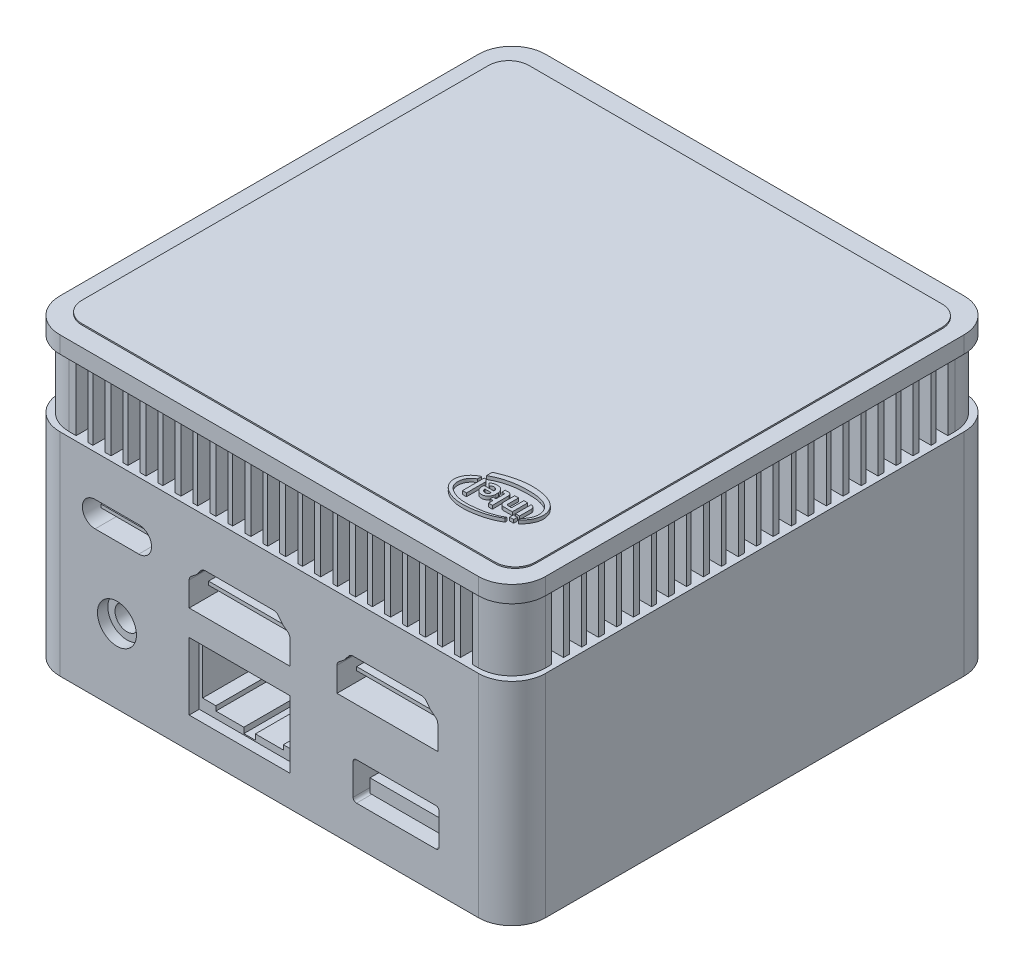
SolidWorks part; units mm, degrees
ref_plane "前视基准面" through (0, 0, 0) normal (0, 0, 1) x (1, 0, 0)
ref_plane "上视基准面" through (0, 0, 0) normal (0, 1, 0) x (1, 0, 0)
ref_plane "右视基准面" through (0, 0, 0) normal (1, 0, 0) x (0, 0, -1)
sketch "草图1" plane through (0, 0, 0) normal (0, 1, 0) x (1, 0, 0)
  line L1 (-31.15, 36.15) -> (31.15, 36.15)
  line L2 (-36.15, 31.15) -> (-36.15, -31.15)
  line L3 (-31.15, -36.15) -> (31.15, -36.15)
  line L4 (36.15, 31.15) -> (36.15, -31.15)
  line L5 (-36.15, 36.15) -> (36.15, -36.15) construction
  line L6 (-36.15, -36.15) -> (36.15, 36.15) construction
  arc A0 (31.15, -36.15) -> (36.15, -31.15) centre (31.15, -31.15) ccw
  arc A1 (-36.15, -31.15) -> (-31.15, -36.15) centre (-31.15, -31.15) ccw
  arc A2 (-31.15, 36.15) -> (-36.15, 31.15) centre (-31.15, 31.15) ccw
  arc A3 (31.15, 36.15) -> (36.15, 31.15) centre (31.15, 31.15) cw
  point P0 (0, 0)
  dimension "D2" = 5
  dimension "D3" = 5
  dimension "D4" = 5
  dimension "D5" = 5
  dimension "D1" = 72.3
extrude "凸台-拉伸1" add sketch "草图1" along normal blind 31.5
sketch "草图2" plane through (0, 31.5, 0) normal (0, 1, 0) x (1, 0, 0)
  line L1 (-30.45, 35.45) -> (30.45, 35.45)
  line L2 (-35.45, 30.45) -> (-35.45, -30.45)
  line L3 (-30.45, -35.45) -> (30.45, -35.45)
  line L4 (35.45, 30.45) -> (35.45, -30.45)
  line L5 (-35.45, 35.45) -> (35.45, -35.45) construction
  line L6 (-35.45, -35.45) -> (35.45, 35.45) construction
  arc A0 (-30.45, 35.45) -> (-35.45, 30.45) centre (-30.45, 30.45) ccw
  arc A1 (-35.45, -30.45) -> (-30.45, -35.45) centre (-30.45, -30.45) ccw
  arc A2 (30.45, -35.45) -> (35.45, -30.45) centre (30.45, -30.45) ccw
  arc A3 (30.45, 35.45) -> (35.45, 30.45) centre (30.45, 30.45) cw
  point P0 (0, 0)
  dimension "D2" = 5
  dimension "D3" = 5
  dimension "D4" = 5
  dimension "D5" = 5
  dimension "D1" = 70.9
extrude "凸台-拉伸2" add sketch "草图2" along normal blind 10
sketch "草图3" plane through (0, 41.5, 0) normal (0, 1, 0) x (1, 0, 0)
  line L0 (30.45, 35.45) -> (-30.45, 35.45) construction
  line L1 (-29.5755, 37.7794) -> (-27.7755, 37.7794)
  line L2 (-29.5755, 37.7794) -> (-29.5755, 33.1206)
  line L3 (-29.5755, 33.1206) -> (-27.7755, 33.1206)
  line L4 (-27.7755, 37.7794) -> (-27.7755, 33.1206)
  line L5 (-29.5755, 37.7794) -> (-27.7755, 33.1206) construction
  line L6 (-29.5755, 33.1206) -> (-27.7755, 37.7794) construction
  line L7 (-26.8755, 37.7794) -> (-25.0755, 37.7794)
  line L8 (-26.8755, 37.7794) -> (-26.8755, 33.1206)
  line L9 (-26.8755, 33.1206) -> (-25.0755, 33.1206)
  line L10 (-25.0755, 37.7794) -> (-25.0755, 33.1206)
  line L11 (-21.6755, 37.7794) -> (-19.8755, 37.7794)
  line L12 (-19.8755, 37.7794) -> (-19.8755, 33.1206)
  line L13 (-21.6755, 33.1206) -> (-19.8755, 33.1206)
  line L14 (-21.6755, 37.7794) -> (-21.6755, 33.1206)
  line L15 (-24.3755, 37.7794) -> (-24.3755, 33.1206)
  line L16 (-24.3755, 37.7794) -> (-22.5755, 37.7794)
  line L17 (-22.5755, 37.7794) -> (-22.5755, 33.1206)
  line L18 (-24.3755, 33.1206) -> (-22.5755, 33.1206)
  line L19 (-16.4755, 37.7794) -> (-14.6755, 37.7794)
  line L20 (-14.6755, 37.7794) -> (-14.6755, 33.1206)
  line L21 (-16.4755, 33.1206) -> (-14.6755, 33.1206)
  line L22 (-16.4755, 37.7794) -> (-16.4755, 33.1206)
  line L23 (-19.1755, 37.7794) -> (-19.1755, 33.1206)
  line L24 (-19.1755, 37.7794) -> (-17.3755, 37.7794)
  line L25 (-17.3755, 37.7794) -> (-17.3755, 33.1206)
  line L26 (-19.1755, 33.1206) -> (-17.3755, 33.1206)
  line L27 (-11.2755, 37.7794) -> (-9.4755, 37.7794)
  line L28 (-9.4755, 37.7794) -> (-9.4755, 33.1206)
  line L29 (-11.2755, 33.1206) -> (-9.4755, 33.1206)
  line L30 (-11.2755, 37.7794) -> (-11.2755, 33.1206)
  line L31 (-13.9755, 37.7794) -> (-13.9755, 33.1206)
  line L32 (-13.9755, 37.7794) -> (-12.1755, 37.7794)
  line L33 (-12.1755, 37.7794) -> (-12.1755, 33.1206)
  line L34 (-13.9755, 33.1206) -> (-12.1755, 33.1206)
  line L35 (-6.0755, 37.7794) -> (-4.2755, 37.7794)
  line L36 (-4.2755, 37.7794) -> (-4.2755, 33.1206)
  line L37 (-6.0755, 33.1206) -> (-4.2755, 33.1206)
  line L38 (-6.0755, 37.7794) -> (-6.0755, 33.1206)
  line L39 (-8.7755, 37.7794) -> (-8.7755, 33.1206)
  line L40 (-8.7755, 37.7794) -> (-6.9755, 37.7794)
  line L41 (-6.9755, 37.7794) -> (-6.9755, 33.1206)
  line L42 (-8.7755, 33.1206) -> (-6.9755, 33.1206)
  line L43 (-0.8755, 37.7794) -> (0.9245, 37.7794)
  line L44 (0.9245, 37.7794) -> (0.9245, 33.1206)
  line L45 (-0.8755, 33.1206) -> (0.9245, 33.1206)
  line L46 (-0.8755, 37.7794) -> (-0.8755, 33.1206)
  line L47 (-3.5755, 37.7794) -> (-3.5755, 33.1206)
  line L48 (-3.5755, 37.7794) -> (-1.7755, 37.7794)
  line L49 (-1.7755, 37.7794) -> (-1.7755, 33.1206)
  line L50 (-3.5755, 33.1206) -> (-1.7755, 33.1206)
  line L51 (4.3245, 37.7794) -> (6.1245, 37.7794)
  line L52 (6.1245, 37.7794) -> (6.1245, 33.1206)
  line L53 (4.3245, 33.1206) -> (6.1245, 33.1206)
  line L54 (4.3245, 37.7794) -> (4.3245, 33.1206)
  line L55 (1.6245, 37.7794) -> (1.6245, 33.1206)
  line L56 (1.6245, 37.7794) -> (3.4245, 37.7794)
  line L57 (3.4245, 37.7794) -> (3.4245, 33.1206)
  line L58 (1.6245, 33.1206) -> (3.4245, 33.1206)
  line L59 (9.5245, 37.7794) -> (11.3245, 37.7794)
  line L60 (11.3245, 37.7794) -> (11.3245, 33.1206)
  line L61 (9.5245, 33.1206) -> (11.3245, 33.1206)
  line L62 (9.5245, 37.7794) -> (9.5245, 33.1206)
  line L63 (6.8245, 37.7794) -> (6.8245, 33.1206)
  line L64 (6.8245, 37.7794) -> (8.6245, 37.7794)
  line L65 (8.6245, 37.7794) -> (8.6245, 33.1206)
  line L66 (6.8245, 33.1206) -> (8.6245, 33.1206)
  line L67 (14.7245, 37.7794) -> (16.5245, 37.7794)
  line L68 (16.5245, 37.7794) -> (16.5245, 33.1206)
  line L69 (14.7245, 33.1206) -> (16.5245, 33.1206)
  line L70 (14.7245, 37.7794) -> (14.7245, 33.1206)
  line L71 (12.0245, 37.7794) -> (12.0245, 33.1206)
  line L72 (12.0245, 37.7794) -> (13.8245, 37.7794)
  line L73 (13.8245, 37.7794) -> (13.8245, 33.1206)
  line L74 (12.0245, 33.1206) -> (13.8245, 33.1206)
  line L75 (19.9245, 37.7794) -> (21.7245, 37.7794)
  line L76 (21.7245, 37.7794) -> (21.7245, 33.1206)
  line L77 (19.9245, 33.1206) -> (21.7245, 33.1206)
  line L78 (19.9245, 37.7794) -> (19.9245, 33.1206)
  line L79 (17.2245, 37.7794) -> (17.2245, 33.1206)
  line L80 (17.2245, 37.7794) -> (19.0245, 37.7794)
  line L81 (19.0245, 37.7794) -> (19.0245, 33.1206)
  line L82 (17.2245, 33.1206) -> (19.0245, 33.1206)
  line L83 (25.1245, 37.7794) -> (26.9245, 37.7794)
  line L84 (26.9245, 37.7794) -> (26.9245, 33.1206)
  line L85 (25.1245, 33.1206) -> (26.9245, 33.1206)
  line L86 (25.1245, 37.7794) -> (25.1245, 33.1206)
  line L87 (22.4245, 37.7794) -> (22.4245, 33.1206)
  line L88 (22.4245, 37.7794) -> (24.2245, 37.7794)
  line L89 (24.2245, 37.7794) -> (24.2245, 33.1206)
  line L90 (22.4245, 33.1206) -> (24.2245, 33.1206)
  line L95 (27.6245, 37.7794) -> (27.6245, 33.1206)
  line L96 (27.6245, 37.7794) -> (29.4245, 37.7794)
  line L97 (29.4245, 37.7794) -> (29.4245, 33.1206)
  line L98 (27.6245, 33.1206) -> (29.4245, 33.1206)
  line L99 (30.3245, 37.7794) -> (32.1245, 37.7794) [skipped]
  line L100 (32.1245, 37.7794) -> (32.1245, 33.1206) [skipped]
  line L101 (30.3245, 33.1206) -> (32.1245, 33.1206) [skipped]
  line L102 (30.3245, 37.7794) -> (30.3245, 33.1206) [skipped]
  line L103 (0, 0) -> (30.3531, 30.3531) construction
  line L104 (0, 0) -> (-19.9439, 19.9439) construction
  line L105 (-33.1206, 29.5755) -> (-37.7794, 27.7755) construction
  line L106 (-37.7794, 29.5755) -> (-33.1206, 27.7755) construction
  line L107 (-33.1206, -27.6245) -> (-33.1206, -29.4245)
  line L108 (-37.7794, -29.4245) -> (-33.1206, -29.4245)
  line L109 (-37.7794, -27.6245) -> (-37.7794, -29.4245)
  line L110 (-37.7794, -27.6245) -> (-33.1206, -27.6245)
  line L111 (-33.1206, -22.4245) -> (-33.1206, -24.2245)
  line L112 (-37.7794, -24.2245) -> (-33.1206, -24.2245)
  line L113 (-37.7794, -22.4245) -> (-37.7794, -24.2245)
  line L114 (-37.7794, -22.4245) -> (-33.1206, -22.4245)
  line L115 (-37.7794, -25.1245) -> (-33.1206, -25.1245)
  line L116 (-33.1206, -25.1245) -> (-33.1206, -26.9245)
  line L117 (-37.7794, -26.9245) -> (-33.1206, -26.9245)
  line L118 (-37.7794, -25.1245) -> (-37.7794, -26.9245)
  line L119 (-33.1206, -17.2245) -> (-33.1206, -19.0245)
  line L120 (-37.7794, -19.0245) -> (-33.1206, -19.0245)
  line L121 (-37.7794, -17.2245) -> (-37.7794, -19.0245)
  line L122 (-37.7794, -17.2245) -> (-33.1206, -17.2245)
  line L123 (-37.7794, -19.9245) -> (-33.1206, -19.9245)
  line L124 (-33.1206, -19.9245) -> (-33.1206, -21.7245)
  line L125 (-37.7794, -21.7245) -> (-33.1206, -21.7245)
  line L126 (-37.7794, -19.9245) -> (-37.7794, -21.7245)
  line L127 (-33.1206, -12.0245) -> (-33.1206, -13.8245)
  line L128 (-37.7794, -13.8245) -> (-33.1206, -13.8245)
  line L129 (-37.7794, -12.0245) -> (-37.7794, -13.8245)
  line L130 (-37.7794, -12.0245) -> (-33.1206, -12.0245)
  line L131 (-37.7794, -14.7245) -> (-33.1206, -14.7245)
  line L132 (-33.1206, -14.7245) -> (-33.1206, -16.5245)
  line L133 (-37.7794, -16.5245) -> (-33.1206, -16.5245)
  line L134 (-37.7794, -14.7245) -> (-37.7794, -16.5245)
  line L135 (-33.1206, -6.8245) -> (-33.1206, -8.6245)
  line L136 (-37.7794, -8.6245) -> (-33.1206, -8.6245)
  line L137 (-37.7794, -6.8245) -> (-37.7794, -8.6245)
  line L138 (-37.7794, -6.8245) -> (-33.1206, -6.8245)
  line L139 (-37.7794, -9.5245) -> (-33.1206, -9.5245)
  line L140 (-33.1206, -9.5245) -> (-33.1206, -11.3245)
  line L141 (-37.7794, -11.3245) -> (-33.1206, -11.3245)
  line L142 (-37.7794, -9.5245) -> (-37.7794, -11.3245)
  line L143 (-33.1206, -1.6245) -> (-33.1206, -3.4245)
  line L144 (-37.7794, -3.4245) -> (-33.1206, -3.4245)
  line L145 (-37.7794, -1.6245) -> (-37.7794, -3.4245)
  line L146 (-37.7794, -1.6245) -> (-33.1206, -1.6245)
  line L147 (-37.7794, -4.3245) -> (-33.1206, -4.3245)
  line L148 (-33.1206, -4.3245) -> (-33.1206, -6.1245)
  line L149 (-37.7794, -6.1245) -> (-33.1206, -6.1245)
  line L150 (-37.7794, -4.3245) -> (-37.7794, -6.1245)
  line L151 (-33.1206, 3.5755) -> (-33.1206, 1.7755)
  line L152 (-37.7794, 1.7755) -> (-33.1206, 1.7755)
  line L153 (-37.7794, 3.5755) -> (-37.7794, 1.7755)
  line L154 (-37.7794, 3.5755) -> (-33.1206, 3.5755)
  line L155 (-37.7794, 0.8755) -> (-33.1206, 0.8755)
  line L156 (-33.1206, 0.8755) -> (-33.1206, -0.9245)
  line L157 (-37.7794, -0.9245) -> (-33.1206, -0.9245)
  line L158 (-37.7794, 0.8755) -> (-37.7794, -0.9245)
  line L159 (-33.1206, 8.7755) -> (-33.1206, 6.9755)
  line L160 (-37.7794, 6.9755) -> (-33.1206, 6.9755)
  line L161 (-37.7794, 8.7755) -> (-37.7794, 6.9755)
  line L162 (-37.7794, 8.7755) -> (-33.1206, 8.7755)
  line L163 (-37.7794, 6.0755) -> (-33.1206, 6.0755)
  line L164 (-33.1206, 6.0755) -> (-33.1206, 4.2755)
  line L165 (-37.7794, 4.2755) -> (-33.1206, 4.2755)
  line L166 (-37.7794, 6.0755) -> (-37.7794, 4.2755)
  line L167 (-33.1206, 13.9755) -> (-33.1206, 12.1755)
  line L168 (-37.7794, 12.1755) -> (-33.1206, 12.1755)
  line L169 (-37.7794, 13.9755) -> (-37.7794, 12.1755)
  line L170 (-37.7794, 13.9755) -> (-33.1206, 13.9755)
  line L171 (-37.7794, 11.2755) -> (-33.1206, 11.2755)
  line L172 (-33.1206, 11.2755) -> (-33.1206, 9.4755)
  line L173 (-37.7794, 9.4755) -> (-33.1206, 9.4755)
  line L174 (-37.7794, 11.2755) -> (-37.7794, 9.4755)
  line L175 (-33.1206, 19.1755) -> (-33.1206, 17.3755)
  line L176 (-37.7794, 17.3755) -> (-33.1206, 17.3755)
  line L177 (-37.7794, 19.1755) -> (-37.7794, 17.3755)
  line L178 (-37.7794, 19.1755) -> (-33.1206, 19.1755)
  line L179 (-37.7794, 16.4755) -> (-33.1206, 16.4755)
  line L180 (-33.1206, 16.4755) -> (-33.1206, 14.6755)
  line L181 (-37.7794, 14.6755) -> (-33.1206, 14.6755)
  line L182 (-37.7794, 16.4755) -> (-37.7794, 14.6755)
  line L183 (-33.1206, 24.3755) -> (-33.1206, 22.5755)
  line L184 (-37.7794, 22.5755) -> (-33.1206, 22.5755)
  line L185 (-37.7794, 24.3755) -> (-37.7794, 22.5755)
  line L186 (-37.7794, 24.3755) -> (-33.1206, 24.3755)
  line L187 (-37.7794, 21.6755) -> (-33.1206, 21.6755)
  line L188 (-33.1206, 21.6755) -> (-33.1206, 19.8755)
  line L189 (-37.7794, 19.8755) -> (-33.1206, 19.8755)
  line L190 (-37.7794, 21.6755) -> (-37.7794, 19.8755)
  line L191 (-37.7794, 25.0755) -> (-33.1206, 25.0755)
  line L192 (-33.1206, 26.8755) -> (-33.1206, 25.0755)
  line L193 (-37.7794, 26.8755) -> (-33.1206, 26.8755)
  line L194 (-37.7794, 26.8755) -> (-37.7794, 25.0755)
  line L195 (-37.7794, 27.7755) -> (-33.1206, 27.7755)
  line L196 (-33.1206, 29.5755) -> (-33.1206, 27.7755)
  line L197 (-37.7794, 29.5755) -> (-33.1206, 29.5755)
  line L198 (-37.7794, 29.5755) -> (-37.7794, 27.7755)
  line L199 (29.5755, -37.7794) -> (27.7755, -33.1206) construction
  line L200 (29.5755, -33.1206) -> (27.7755, -37.7794) construction
  line L201 (29.5755, -37.7794) -> (27.7755, -37.7794)
  line L202 (29.5755, -37.7794) -> (29.5755, -33.1206)
  line L203 (29.5755, -33.1206) -> (27.7755, -33.1206)
  line L204 (27.7755, -37.7794) -> (27.7755, -33.1206)
  line L205 (26.8755, -37.7794) -> (25.0755, -37.7794)
  line L206 (26.8755, -37.7794) -> (26.8755, -33.1206)
  line L207 (26.8755, -33.1206) -> (25.0755, -33.1206)
  line L208 (25.0755, -37.7794) -> (25.0755, -33.1206)
  line L209 (21.6755, -37.7794) -> (19.8755, -37.7794)
  line L210 (19.8755, -37.7794) -> (19.8755, -33.1206)
  line L211 (21.6755, -33.1206) -> (19.8755, -33.1206)
  line L212 (21.6755, -37.7794) -> (21.6755, -33.1206)
  line L213 (24.3755, -37.7794) -> (24.3755, -33.1206)
  line L214 (24.3755, -37.7794) -> (22.5755, -37.7794)
  line L215 (22.5755, -37.7794) -> (22.5755, -33.1206)
  line L216 (24.3755, -33.1206) -> (22.5755, -33.1206)
  line L217 (16.4755, -37.7794) -> (14.6755, -37.7794)
  line L218 (14.6755, -37.7794) -> (14.6755, -33.1206)
  line L219 (16.4755, -33.1206) -> (14.6755, -33.1206)
  line L220 (16.4755, -37.7794) -> (16.4755, -33.1206)
  line L221 (19.1755, -37.7794) -> (19.1755, -33.1206)
  line L222 (19.1755, -37.7794) -> (17.3755, -37.7794)
  line L223 (17.3755, -37.7794) -> (17.3755, -33.1206)
  line L224 (19.1755, -33.1206) -> (17.3755, -33.1206)
  line L225 (11.2755, -37.7794) -> (9.4755, -37.7794)
  line L226 (9.4755, -37.7794) -> (9.4755, -33.1206)
  line L227 (11.2755, -33.1206) -> (9.4755, -33.1206)
  line L228 (11.2755, -37.7794) -> (11.2755, -33.1206)
  line L229 (13.9755, -37.7794) -> (13.9755, -33.1206)
  line L230 (13.9755, -37.7794) -> (12.1755, -37.7794)
  line L231 (12.1755, -37.7794) -> (12.1755, -33.1206)
  line L232 (13.9755, -33.1206) -> (12.1755, -33.1206)
  line L233 (6.0755, -37.7794) -> (4.2755, -37.7794)
  line L234 (4.2755, -37.7794) -> (4.2755, -33.1206)
  line L235 (6.0755, -33.1206) -> (4.2755, -33.1206)
  line L236 (6.0755, -37.7794) -> (6.0755, -33.1206)
  line L237 (8.7755, -37.7794) -> (8.7755, -33.1206)
  line L238 (8.7755, -37.7794) -> (6.9755, -37.7794)
  line L239 (6.9755, -37.7794) -> (6.9755, -33.1206)
  line L240 (8.7755, -33.1206) -> (6.9755, -33.1206)
  line L241 (0.8755, -37.7794) -> (-0.9245, -37.7794)
  line L242 (-0.9245, -37.7794) -> (-0.9245, -33.1206)
  line L243 (0.8755, -33.1206) -> (-0.9245, -33.1206)
  line L244 (0.8755, -37.7794) -> (0.8755, -33.1206)
  line L245 (3.5755, -37.7794) -> (3.5755, -33.1206)
  line L246 (3.5755, -37.7794) -> (1.7755, -37.7794)
  line L247 (1.7755, -37.7794) -> (1.7755, -33.1206)
  line L248 (3.5755, -33.1206) -> (1.7755, -33.1206)
  line L249 (-4.3245, -37.7794) -> (-6.1245, -37.7794)
  line L250 (-6.1245, -37.7794) -> (-6.1245, -33.1206)
  line L251 (-4.3245, -33.1206) -> (-6.1245, -33.1206)
  line L252 (-4.3245, -37.7794) -> (-4.3245, -33.1206)
  line L253 (-1.6245, -37.7794) -> (-1.6245, -33.1206)
  line L254 (-1.6245, -37.7794) -> (-3.4245, -37.7794)
  line L255 (-3.4245, -37.7794) -> (-3.4245, -33.1206)
  line L256 (-1.6245, -33.1206) -> (-3.4245, -33.1206)
  line L257 (-9.5245, -37.7794) -> (-11.3245, -37.7794)
  line L258 (-11.3245, -37.7794) -> (-11.3245, -33.1206)
  line L259 (-9.5245, -33.1206) -> (-11.3245, -33.1206)
  line L260 (-9.5245, -37.7794) -> (-9.5245, -33.1206)
  line L261 (-6.8245, -37.7794) -> (-6.8245, -33.1206)
  line L262 (-6.8245, -37.7794) -> (-8.6245, -37.7794)
  line L263 (-8.6245, -37.7794) -> (-8.6245, -33.1206)
  line L264 (-6.8245, -33.1206) -> (-8.6245, -33.1206)
  line L265 (-14.7245, -37.7794) -> (-16.5245, -37.7794)
  line L266 (-16.5245, -37.7794) -> (-16.5245, -33.1206)
  line L267 (-14.7245, -33.1206) -> (-16.5245, -33.1206)
  line L268 (-14.7245, -37.7794) -> (-14.7245, -33.1206)
  line L269 (-12.0245, -37.7794) -> (-12.0245, -33.1206)
  line L270 (-12.0245, -37.7794) -> (-13.8245, -37.7794)
  line L271 (-13.8245, -37.7794) -> (-13.8245, -33.1206)
  line L272 (-12.0245, -33.1206) -> (-13.8245, -33.1206)
  line L273 (-19.9245, -37.7794) -> (-21.7245, -37.7794)
  line L274 (-21.7245, -37.7794) -> (-21.7245, -33.1206)
  line L275 (-19.9245, -33.1206) -> (-21.7245, -33.1206)
  line L276 (-19.9245, -37.7794) -> (-19.9245, -33.1206)
  line L277 (-17.2245, -37.7794) -> (-17.2245, -33.1206)
  line L278 (-17.2245, -37.7794) -> (-19.0245, -37.7794)
  line L279 (-19.0245, -37.7794) -> (-19.0245, -33.1206)
  line L280 (-17.2245, -33.1206) -> (-19.0245, -33.1206)
  line L281 (-25.1245, -37.7794) -> (-26.9245, -37.7794)
  line L282 (-26.9245, -37.7794) -> (-26.9245, -33.1206)
  line L283 (-25.1245, -33.1206) -> (-26.9245, -33.1206)
  line L284 (-25.1245, -37.7794) -> (-25.1245, -33.1206)
  line L285 (-22.4245, -37.7794) -> (-22.4245, -33.1206)
  line L286 (-22.4245, -37.7794) -> (-24.2245, -37.7794)
  line L287 (-24.2245, -37.7794) -> (-24.2245, -33.1206)
  line L288 (-22.4245, -33.1206) -> (-24.2245, -33.1206)
  line L289 (-27.6245, -37.7794) -> (-27.6245, -33.1206)
  line L290 (-27.6245, -37.7794) -> (-29.4245, -37.7794)
  line L291 (-29.4245, -37.7794) -> (-29.4245, -33.1206)
  line L292 (-27.6245, -33.1206) -> (-29.4245, -33.1206)
  line L293 (33.1206, -29.5755) -> (37.7794, -27.7755) construction
  line L294 (37.7794, -29.5755) -> (33.1206, -27.7755) construction
  line L295 (33.1206, 27.6245) -> (33.1206, 29.4245)
  line L296 (37.7794, 29.4245) -> (33.1206, 29.4245)
  line L297 (37.7794, 27.6245) -> (37.7794, 29.4245)
  line L298 (37.7794, 27.6245) -> (33.1206, 27.6245)
  line L299 (33.1206, 22.4245) -> (33.1206, 24.2245)
  line L300 (37.7794, 24.2245) -> (33.1206, 24.2245)
  line L301 (37.7794, 22.4245) -> (37.7794, 24.2245)
  line L302 (37.7794, 22.4245) -> (33.1206, 22.4245)
  line L303 (37.7794, 25.1245) -> (33.1206, 25.1245)
  line L304 (33.1206, 25.1245) -> (33.1206, 26.9245)
  line L305 (37.7794, 26.9245) -> (33.1206, 26.9245)
  line L306 (37.7794, 25.1245) -> (37.7794, 26.9245)
  line L307 (33.1206, 17.2245) -> (33.1206, 19.0245)
  line L308 (37.7794, 19.0245) -> (33.1206, 19.0245)
  line L309 (37.7794, 17.2245) -> (37.7794, 19.0245)
  line L310 (37.7794, 17.2245) -> (33.1206, 17.2245)
  line L311 (37.7794, 19.9245) -> (33.1206, 19.9245)
  line L312 (33.1206, 19.9245) -> (33.1206, 21.7245)
  line L313 (37.7794, 21.7245) -> (33.1206, 21.7245)
  line L314 (37.7794, 19.9245) -> (37.7794, 21.7245)
  line L315 (33.1206, 12.0245) -> (33.1206, 13.8245)
  line L316 (37.7794, 13.8245) -> (33.1206, 13.8245)
  line L317 (37.7794, 12.0245) -> (37.7794, 13.8245)
  line L318 (37.7794, 12.0245) -> (33.1206, 12.0245)
  line L319 (37.7794, 14.7245) -> (33.1206, 14.7245)
  line L320 (33.1206, 14.7245) -> (33.1206, 16.5245)
  line L321 (37.7794, 16.5245) -> (33.1206, 16.5245)
  line L322 (37.7794, 14.7245) -> (37.7794, 16.5245)
  line L323 (33.1206, 6.8245) -> (33.1206, 8.6245)
  line L324 (37.7794, 8.6245) -> (33.1206, 8.6245)
  line L325 (37.7794, 6.8245) -> (37.7794, 8.6245)
  line L326 (37.7794, 6.8245) -> (33.1206, 6.8245)
  line L327 (37.7794, 9.5245) -> (33.1206, 9.5245)
  line L328 (33.1206, 9.5245) -> (33.1206, 11.3245)
  line L329 (37.7794, 11.3245) -> (33.1206, 11.3245)
  line L330 (37.7794, 9.5245) -> (37.7794, 11.3245)
  line L331 (33.1206, 1.6245) -> (33.1206, 3.4245)
  line L332 (37.7794, 3.4245) -> (33.1206, 3.4245)
  line L333 (37.7794, 1.6245) -> (37.7794, 3.4245)
  line L334 (37.7794, 1.6245) -> (33.1206, 1.6245)
  line L335 (37.7794, 4.3245) -> (33.1206, 4.3245)
  line L336 (33.1206, 4.3245) -> (33.1206, 6.1245)
  line L337 (37.7794, 6.1245) -> (33.1206, 6.1245)
  line L338 (37.7794, 4.3245) -> (37.7794, 6.1245)
  line L339 (33.1206, -3.5755) -> (33.1206, -1.7755)
  line L340 (37.7794, -1.7755) -> (33.1206, -1.7755)
  line L341 (37.7794, -3.5755) -> (37.7794, -1.7755)
  line L342 (37.7794, -3.5755) -> (33.1206, -3.5755)
  line L343 (37.7794, -0.8755) -> (33.1206, -0.8755)
  line L344 (33.1206, -0.8755) -> (33.1206, 0.9245)
  line L345 (37.7794, 0.9245) -> (33.1206, 0.9245)
  line L346 (37.7794, -0.8755) -> (37.7794, 0.9245)
  line L347 (33.1206, -8.7755) -> (33.1206, -6.9755)
  line L348 (37.7794, -6.9755) -> (33.1206, -6.9755)
  line L349 (37.7794, -8.7755) -> (37.7794, -6.9755)
  line L350 (37.7794, -8.7755) -> (33.1206, -8.7755)
  line L351 (37.7794, -6.0755) -> (33.1206, -6.0755)
  line L352 (33.1206, -6.0755) -> (33.1206, -4.2755)
  line L353 (37.7794, -4.2755) -> (33.1206, -4.2755)
  line L354 (37.7794, -6.0755) -> (37.7794, -4.2755)
  line L355 (33.1206, -13.9755) -> (33.1206, -12.1755)
  line L356 (37.7794, -12.1755) -> (33.1206, -12.1755)
  line L357 (37.7794, -13.9755) -> (37.7794, -12.1755)
  line L358 (37.7794, -13.9755) -> (33.1206, -13.9755)
  line L359 (37.7794, -11.2755) -> (33.1206, -11.2755)
  line L360 (33.1206, -11.2755) -> (33.1206, -9.4755)
  line L361 (37.7794, -9.4755) -> (33.1206, -9.4755)
  line L362 (37.7794, -11.2755) -> (37.7794, -9.4755)
  line L363 (33.1206, -19.1755) -> (33.1206, -17.3755)
  line L364 (37.7794, -17.3755) -> (33.1206, -17.3755)
  line L365 (37.7794, -19.1755) -> (37.7794, -17.3755)
  line L366 (37.7794, -19.1755) -> (33.1206, -19.1755)
  line L367 (37.7794, -16.4755) -> (33.1206, -16.4755)
  line L368 (33.1206, -16.4755) -> (33.1206, -14.6755)
  line L369 (37.7794, -14.6755) -> (33.1206, -14.6755)
  line L370 (37.7794, -16.4755) -> (37.7794, -14.6755)
  line L371 (33.1206, -24.3755) -> (33.1206, -22.5755)
  line L372 (37.7794, -22.5755) -> (33.1206, -22.5755)
  line L373 (37.7794, -24.3755) -> (37.7794, -22.5755)
  line L374 (37.7794, -24.3755) -> (33.1206, -24.3755)
  line L375 (37.7794, -21.6755) -> (33.1206, -21.6755)
  line L376 (33.1206, -21.6755) -> (33.1206, -19.8755)
  line L377 (37.7794, -19.8755) -> (33.1206, -19.8755)
  line L378 (37.7794, -21.6755) -> (37.7794, -19.8755)
  line L379 (37.7794, -25.0755) -> (33.1206, -25.0755)
  line L380 (33.1206, -26.8755) -> (33.1206, -25.0755)
  line L381 (37.7794, -26.8755) -> (33.1206, -26.8755)
  line L382 (37.7794, -26.8755) -> (37.7794, -25.0755)
  line L383 (37.7794, -27.7755) -> (33.1206, -27.7755)
  line L384 (33.1206, -29.5755) -> (33.1206, -27.7755)
  line L385 (37.7794, -29.5755) -> (33.1206, -29.5755)
  line L386 (37.7794, -29.5755) -> (37.7794, -27.7755)
  point P0 (-28.6755, 35.45)
  point P202 (-35.45, 28.6755)
  point P295 (28.6755, -35.45)
  point P388 (35.45, -28.6755)
  dimension "D1" = 1.8
  dimension "D2" = 0.9
  dimension "D3" = 1.8
  dimension "D4" = 12
extrude "切除-拉伸1" cut sketch "草图3" against normal blind 10
sketch "草图4" plane through (0, 41.5, 0) normal (0, 1, 0) x (1, 0, 0)
  line L1 (-31.15, -36.15) -> (31.15, -36.15)
  line L2 (-36.15, -31.15) -> (-36.15, 31.15)
  line L3 (-31.15, 36.15) -> (31.15, 36.15)
  line L4 (36.15, -31.15) -> (36.15, 31.15)
  line L5 (-36.15, -36.15) -> (36.15, 36.15) construction
  line L6 (-36.15, 36.15) -> (36.15, -36.15) construction
  arc A0 (-36.15, 31.15) -> (-31.15, 36.15) centre (-31.15, 31.15) cw
  arc A1 (-31.15, -36.15) -> (-36.15, -31.15) centre (-31.15, -31.15) cw
  arc A2 (31.15, -36.15) -> (36.15, -31.15) centre (31.15, -31.15) ccw
  arc A3 (31.15, 36.15) -> (36.15, 31.15) centre (31.15, 31.15) cw
  point P0 (0, 0)
  dimension "D2" = 5
  dimension "D3" = 5
  dimension "D4" = 5
  dimension "D5" = 5
  dimension "D1" = 72.3
extrude "凸台-拉伸3" add sketch "草图4" along normal blind 2.5
sketch "草图5" plane through (0, 44, 0) normal (0, 1, 0) x (1, 0, 0)
  line L1 (-30.75, 33.2683) -> (30.75, 33.2683)
  line L2 (-33.75, 30.2683) -> (-33.75, -30.2683)
  line L3 (-30.75, -33.2683) -> (30.75, -33.2683)
  line L4 (33.75, 30.2683) -> (33.75, -30.2683)
  line L5 (-33.75, 33.2683) -> (33.75, -33.2683) construction
  line L6 (-33.75, -33.2683) -> (33.75, 33.2683) construction
  arc A0 (-30.75, 33.2683) -> (-33.75, 30.2683) centre (-30.75, 30.2683) ccw
  arc A1 (-33.75, -30.2683) -> (-30.75, -33.2683) centre (-30.75, -30.2683) ccw
  arc A2 (30.75, -33.2683) -> (33.75, -30.2683) centre (30.75, -30.2683) ccw
  arc A3 (30.75, 33.2683) -> (33.75, 30.2683) centre (30.75, 30.2683) cw
  point P0 (0, 0)
  dimension "D2" = 3
  dimension "D3" = 3
  dimension "D4" = 3
  dimension "D5" = 3
  dimension "D1" = 67.5
extrude "凸台-拉伸4" add sketch "草图5" along normal blind 0.2
sketch "草图6" plane through (0, 0, -36.15) normal (0, 0, -1) x (-1, 0, 0)
  line L0 (-31.15, 0) -> (31.15, 0) construction
  line L1 (-36.15, 31.5) -> (-36.15, 0) construction
  circle A0 centre (-20.65, 21) radius 5.2
  circle A1 centre (-20.65, 21) radius 0.75
  dimension "D2" = 10.4
  dimension "D3" = 1.5
  dimension "D1" = 21
  dimension "D4" = 15.5
extrude "切除-拉伸2" cut sketch "草图6" against normal blind 0.5
sketch "草图7" plane through (0, 0, -36.15) normal (0, 0, -1) x (-1, 0, 0)
  line L0 (-31.15, 0) -> (31.15, 0) construction
  line L1 (-7.35, 23) -> (26.15, 23)
  line L2 (-9.35, 21) -> (-9.35, 15)
  line L3 (-7.35, 13) -> (26.15, 13)
  line L4 (28.15, 21) -> (28.15, 15)
  line L5 (-9.35, 23) -> (28.15, 13) construction
  line L6 (-9.35, 13) -> (28.15, 23) construction
  line L7 (36.15, 31.5) -> (36.15, 0) construction
  arc A0 (-7.35, 23) -> (-9.35, 21) centre (-7.35, 21) ccw
  arc A1 (-9.35, 15) -> (-7.35, 13) centre (-7.35, 15) ccw
  arc A2 (26.15, 13) -> (28.15, 15) centre (26.15, 15) ccw
  arc A3 (26.15, 23) -> (28.15, 21) centre (26.15, 21) cw
  point P0 (9.4, 18)
  dimension "D5" = 2
  dimension "D6" = 2
  dimension "D7" = 2
  dimension "D8" = 2
  dimension "D1" = 13
  dimension "D2" = 8
  dimension "D3" = 37.5
  dimension "D4" = 10
extrude "切除-拉伸3" cut sketch "草图7" against normal blind 0.5
sketch "草图8" plane through (0, 0, -35.65) normal (0, 0, -1) x (-1, 0, 0)
  line L0 (-9.35, 21) -> (-9.35, 15) construction
  line L1 (-6.55, 20.8) -> (4.65, 20.8)
  line L2 (-7.35, 20) -> (-7.35, 16)
  line L3 (-6.55, 15.2) -> (4.65, 15.2)
  line L4 (5.45, 20) -> (5.45, 16)
  line L5 (-7.35, 20.8) -> (5.45, 15.2) construction
  line L6 (-7.35, 15.2) -> (5.45, 20.8) construction
  line L7 (-7.35, 13) -> (26.15, 13) construction
  line L9 (14.25, 20.8) -> (25.45, 20.8)
  line L10 (13.45, 20) -> (13.45, 16)
  line L11 (14.25, 15.2) -> (25.45, 15.2)
  line L12 (26.25, 20) -> (26.25, 16)
  arc A0 (25.45, 15.2) -> (26.25, 16) centre (25.45, 16) ccw
  arc A1 (25.45, 20.8) -> (26.25, 20) centre (25.45, 20) cw
  arc A2 (13.45, 16) -> (14.25, 15.2) centre (14.25, 16) ccw
  arc A3 (14.25, 20.8) -> (13.45, 20) centre (14.25, 20) ccw
  arc A4 (4.65, 15.2) -> (5.45, 16) centre (4.65, 16) ccw
  arc A5 (4.65, 20.8) -> (5.45, 20) centre (4.65, 20) cw
  arc A6 (-7.35, 16) -> (-6.55, 15.2) centre (-6.55, 16) ccw
  arc A7 (-6.55, 20.8) -> (-7.35, 20) centre (-6.55, 20) ccw
  point P0 (-0.95, 18)
  point P15 (26.25, 15.2)
  point P18 (26.25, 20.8)
  point P21 (13.45, 15.2)
  dimension "D8" = 0.8
  dimension "D9" = 0.8
  dimension "D10" = 0.8
  dimension "D11" = 0.8
  dimension "D12" = 0.8
  dimension "D13" = 0.8
  dimension "D14" = 0.8
  dimension "D15" = 0.8
  dimension "D1" = 2
  dimension "D2" = 12.8
  dimension "D3" = 2.2
  dimension "D4" = 5.6
  dimension "D5" = 12.8
  dimension "D6" = 5.6
  dimension "D7" = 8
extrude "切除-拉伸4" cut sketch "草图8" against normal blind 13.6 and the other way blind 10
sketch "草图9" plane through (0, 0, -22.05) normal (0, 0, -1) x (-1, 0, 0)
  line L0 (5.45, 16) -> (5.45, 20) construction
  line L1 (-5.85, 19.8) -> (3.95, 19.8)
  line L2 (-5.85, 19.8) -> (-5.85, 18)
  line L3 (-5.85, 18) -> (3.95, 18)
  line L4 (3.95, 19.8) -> (3.95, 18)
  line L5 (-5.85, 19.8) -> (3.95, 18) construction
  line L6 (-5.85, 18) -> (3.95, 19.8) construction
  line L7 (-7.35, 20) -> (-7.35, 16) construction
  line L8 (4.65, 20.8) -> (-6.55, 20.8) construction
  line L9 (-6.55, 15.2) -> (4.65, 15.2) construction
  line L10 (14.95, 19.8) -> (24.75, 19.8)
  line L11 (14.95, 19.8) -> (14.95, 18)
  line L12 (14.95, 18) -> (24.75, 18)
  line L13 (24.75, 19.8) -> (24.75, 18)
  line L14 (26.25, 20) -> (26.25, 16) construction
  line L15 (25.45, 20.8) -> (14.25, 20.8) construction
  point P0 (-0.95, 18.9)
  dimension "D1" = 1.5
  dimension "D2" = 1.5
  dimension "D3" = 1
  dimension "D4" = 2.8
  dimension "D5" = 9.8
  dimension "D6" = 1.8
  dimension "D7" = 1.5
  dimension "D8" = 1
extrude "凸台-拉伸5" add sketch "草图9" along normal blind 12.5
sketch "草图10" plane through (-36.15, 0, 0) normal (-1, 0, 0) x (0, 0, 1)
  line L0 (-31.15, 0) -> (31.15, 0) construction
  line L1 (-15.15, 13) -> (-2.75, 13)
  line L2 (-15.15, 13) -> (-15.15, 11)
  line L3 (-15.15, 11) -> (-2.75, 11)
  line L4 (-2.75, 13) -> (-2.75, 11)
  line L5 (-15.15, 13) -> (-2.75, 11) construction
  line L6 (-15.15, 11) -> (-2.75, 13) construction
  line L7 (-36.15, 31.5) -> (-36.15, 0) construction
  point P0 (-8.95, 12)
  dimension "D1" = 11
  dimension "D2" = 12.4
  dimension "D3" = 2
  dimension "D4" = 21
extrude "切除-拉伸5" cut sketch "草图10" against normal blind 15
sketch "草图12" plane through (-36.15, 0, 0) normal (-1, 0, 0) x (0, 0, 1)
  line L0 (-31.15, 0) -> (31.15, 0) construction
  line L1 (11.35, 15.7) -> (17.65, 15.7)
  line L2 (10.85, 15.2) -> (10.85, 11.7)
  line L3 (11.35, 11.2) -> (17.65, 11.2)
  line L4 (18.15, 15.2) -> (18.15, 11.7)
  line L5 (10.85, 15.7) -> (18.15, 11.2) construction
  line L6 (10.85, 11.2) -> (18.15, 15.7) construction
  line L7 (36.15, 31.5) -> (36.15, 0) construction
  arc A0 (17.65, 11.2) -> (18.15, 11.7) centre (17.65, 11.7) ccw
  arc A1 (17.65, 15.7) -> (18.15, 15.2) centre (17.65, 15.2) cw
  arc A2 (10.85, 11.7) -> (11.35, 11.2) centre (11.35, 11.7) ccw
  arc A3 (11.35, 15.7) -> (10.85, 15.2) centre (11.35, 15.2) ccw
  point P0 (14.5, 13.45)
  dimension "D5" = 0.5
  dimension "D6" = 0.5
  dimension "D7" = 0.5
  dimension "D8" = 0.5
  dimension "D1" = 11.2
  dimension "D2" = 7.3
  dimension "D3" = 4.5
  dimension "D4" = 18
extrude "切除-拉伸6" cut sketch "草图12" against normal blind 5
sketch "草图13" plane through (0, 0, 36.15) normal (0, 0, 1) x (1, 0, 0)
  line L0 (-31.15, 0) -> (31.15, 0) construction
  line L1 (-36.15, 31.5) -> (-36.15, 0) construction
  line L2 (-25.9, 23.5) -> (-19.4, 23.5) construction
  line L3 (-25.9, 25.4) -> (-19.4, 25.4)
  line L4 (-25.9, 21.6) -> (-19.4, 21.6)
  line L5 (-22.4245, 31.5) -> (-21.7245, 31.5) construction
  line L6 (-11.9, 22.0069) -> (-11.9, 18.4)
  line L7 (-11.9, 14.6) -> (3.1, 14.6)
  line L8 (-11.9, 14.6) -> (-11.9, 4.6)
  line L9 (-11.9, 4.6) -> (3.1, 4.6)
  line L10 (3.1, 14.6) -> (3.1, 4.6)
  line L11 (-11.9, 14.6) -> (3.1, 4.6) construction
  line L12 (-11.9, 4.6) -> (3.1, 14.6) construction
  line L13 (-11.9, 18.4) -> (3.1, 18.4)
  line L14 (3.1, 18.4) -> (3.1, 22.0069)
  line L15 (2.7889, 22.6402) -> (2.0956, 23.1753)
  line L16 (1.9512, 23.3197) -> (1.3575, 24.0889)
  line L17 (0.7242, 24.4) -> (-9.5242, 24.4)
  line L18 (-10.1575, 24.0889) -> (-10.7512, 23.3197)
  line L19 (-10.8956, 23.1753) -> (-11.5889, 22.6402)
  line L20 (2.0141, 23.2382) -> (-10.8141, 23.2382) construction
  line L21 (10.1, 22.0069) -> (10.1, 18.4)
  line L22 (10.1, 18.4) -> (25.1, 18.4)
  line L23 (25.1, 18.4) -> (25.1, 22.0069)
  line L24 (24.7889, 22.6402) -> (24.0956, 23.1753)
  line L25 (23.9512, 23.3197) -> (23.3575, 24.0889)
  line L26 (22.7242, 24.4) -> (12.4758, 24.4)
  line L27 (11.8425, 24.0889) -> (11.2488, 23.3197)
  line L28 (11.1044, 23.1753) -> (10.4111, 22.6402)
  line L30 (13, 11.3) -> (24.8, 11.3)
  line L31 (12.5, 10.8) -> (12.5, 6.2)
  line L32 (13, 5.7) -> (24.8, 5.7)
  line L33 (25.3, 10.8) -> (25.3, 6.2)
  line L34 (12.5, 11.3) -> (25.3, 5.7) construction
  line L35 (12.5, 5.7) -> (25.3, 11.3) construction
  circle A0 centre (-22.65, 11) radius 2.9
  arc A1 (-25.9, 25.4) -> (-25.9, 21.6) centre (-25.9, 23.5) ccw
  arc A2 (-19.4, 21.6) -> (-19.4, 25.4) centre (-19.4, 23.5) ccw
  arc A3 (24.8, 11.3) -> (25.3, 10.8) centre (24.8, 10.8) cw
  arc A4 (24.8, 5.7) -> (25.3, 6.2) centre (24.8, 6.2) ccw
  arc A5 (12.5, 6.2) -> (13, 5.7) centre (13, 6.2) ccw
  arc A6 (13, 11.3) -> (12.5, 10.8) centre (13, 10.8) ccw
  arc A7 (3.1, 22.0069) -> (2.7889, 22.6402) centre (2.3, 22.0069) ccw
  arc A8 (-11.9, 22.0069) -> (-11.5889, 22.6402) centre (-11.1, 22.0069) cw
  arc A9 (-10.7512, 23.3197) -> (-10.8956, 23.1753) centre (-11.3845, 23.8086) cw
  arc A10 (2.0956, 23.1753) -> (1.9512, 23.3197) centre (2.5845, 23.8086) cw
  arc A11 (1.3575, 24.0889) -> (0.7242, 24.4) centre (0.7242, 23.6) ccw
  arc A12 (-9.5242, 24.4) -> (-10.1575, 24.0889) centre (-9.5242, 23.6) ccw
  arc A13 (25.1, 22.0069) -> (24.7889, 22.6402) centre (24.3, 22.0069) ccw
  arc A14 (24.0956, 23.1753) -> (23.9512, 23.3197) centre (24.5845, 23.8086) cw
  arc A15 (23.3575, 24.0889) -> (22.7242, 24.4) centre (22.7242, 23.6) ccw
  arc A16 (10.1, 22.0069) -> (10.4111, 22.6402) centre (10.9, 22.0069) cw
  arc A17 (11.2488, 23.3197) -> (11.1044, 23.1753) centre (10.6155, 23.8086) cw
  arc A18 (12.4758, 24.4) -> (11.8425, 24.0889) centre (12.4758, 23.6) ccw
  point P8 (-22.65, 23.5)
  point P17 (-4.4, 9.6)
  point P39 (18.9, 8.5)
  point P55 (3.1, 22.4)
  point P74 (23.1173, 24.4)
  point P77 (10.1, 22.4)
  point P80 (11.1859, 23.2382)
  point P83 (12.0827, 24.4)
  dimension "D1" = 5.8
  dimension "D25" = 0.5
  dimension "D26" = 0.5
  dimension "D27" = 0.5
  dimension "D28" = 0.5
  dimension "D29" = 0.8
  dimension "D30" = 0.8
  dimension "D31" = 0.8
  dimension "D32" = 0.8
  dimension "D33" = 0.8
  dimension "D34" = 0.8
  dimension "D35" = 0.8
  dimension "D36" = 0.8
  dimension "D37" = 0.8
  dimension "D38" = 0.8
  dimension "D39" = 0.8
  dimension "D40" = 0.8
  dimension "D2" = 11
  dimension "D3" = 13.5
  dimension "D4" = 13.5
  dimension "D5" = 6.5
  dimension "D6" = 3.8
  dimension "D7" = 6.1
  dimension "D8" = 15
  dimension "D9" = 10
  dimension "D10" = 4.6
  dimension "D11" = 7.5
  dimension "D12" = 3.8
  dimension "D13" = 4
  dimension "D14" = 6
  dimension "D15" = 15
  dimension "D16" = 4
  dimension "D17" = 1.3718
  dimension "D18" = 1.4677
  dimension "D19" = 11.0346
  dimension "D20" = 7
  dimension "D21" = 12.8
  dimension "D22" = 5.6
  dimension "D23" = 5.7
  dimension "D24" = 9.4
extrude "切除-拉伸7" cut sketch "草图13" against normal blind 13.5
sketch "草图14" plane through (0, 0, 22.65) normal (0, 0, 1) x (1, 0, 0)
  line L0 (11.5375, 21.8113) -> (23.808, 21.8113)
  line L1 (-26.5381, 23.7361) -> (-18.8389, 23.7361)
  line L2 (-26.5381, 23.7361) -> (-26.5381, 23.2549)
  line L3 (-26.5381, 23.2549) -> (-18.8389, 23.2549)
  line L4 (-18.8389, 23.7361) -> (-18.8389, 23.2549)
  line L5 (-26.5381, 23.7361) -> (-18.8389, 23.2549) construction
  line L6 (-26.5381, 23.2549) -> (-18.8389, 23.7361) construction
  line L7 (-10.5142, 21.8113) -> (1.7564, 21.8113)
  line L8 (-10.5142, 21.8113) -> (-10.5142, 21.282)
  line L9 (-10.5142, 21.282) -> (1.7564, 21.282)
  line L10 (1.7564, 21.8113) -> (1.7564, 21.282)
  line L11 (-10.5142, 21.8113) -> (1.7564, 21.282) construction
  line L12 (-10.5142, 21.282) -> (1.7564, 21.8113) construction
  line L13 (11.5375, 21.8113) -> (11.5375, 21.282)
  line L14 (11.5375, 21.282) -> (23.808, 21.282)
  line L15 (23.808, 21.8113) -> (23.808, 21.282)
  line L16 (-11.9, 14.6) -> (-11.9, 4.6)
  line L17 (13.5158, 8.4709) -> (24.3894, 8.4709)
  line L18 (13.5158, 8.4709) -> (13.5158, 6.4644)
  line L19 (13.5158, 6.4644) -> (24.3894, 6.4644)
  line L20 (24.3894, 8.4709) -> (24.3894, 6.4644)
  line L21 (13.5158, 8.4709) -> (24.3894, 6.4644) construction
  line L22 (13.5158, 6.4644) -> (24.3894, 8.4709) construction
  line L23 (-11.9, 4.6) -> (3.1, 4.6)
  line L24 (3.1, 4.6) -> (3.1, 14.6)
  line L25 (3.1, 14.6) -> (-11.9, 14.6)
  line L26 (-11.4, 14.0951) -> (-11.4, 6.2943)
  line L27 (-11.4, 6.2943) -> (-9.4205, 6.2943)
  line L28 (-9.4205, 6.2943) -> (-9.4205, 5.6055)
  line L29 (-9.4205, 5.6055) -> (-5.2587, 5.6055)
  line L30 (-5.2587, 5.6055) -> (-5.2587, 4.7788)
  line L31 (-5.2587, 4.7788) -> (-3.5413, 4.7788)
  line L32 (-3.5413, 4.7788) -> (-3.5413, 5.6055)
  line L33 (-3.5413, 5.6055) -> (0.6205, 5.6055)
  line L34 (0.6205, 5.6055) -> (0.6205, 6.2943)
  line L35 (0.6205, 6.2943) -> (2.6, 6.2943)
  line L36 (2.6, 6.2943) -> (2.6, 14.0951)
  line L37 (2.6, 14.0951) -> (-11.4, 14.0951)
  circle A0 centre (-22.65, 11) radius 1.7882
  circle A1 centre (-22.65, 11) radius 2.8518
  point P0 (-22.6885, 23.4955)
  point P5 (-4.3789, 21.5466)
  point P14 (18.9526, 7.4676)
  dimension "D1" = 0.5
  dimension "D2" = 0.5
extrude "凸台-拉伸6" add sketch "草图14" along normal blind 12
sketch "草图15" plane through (0, 0, 0) normal (0, -1, 0) x (1, 0, 0)
  line L1 (-29.25, 29.25) -> (29.25, 29.25) construction
  line L2 (-29.25, 29.25) -> (-29.25, -29.25) construction
  line L3 (-29.25, -29.25) -> (29.25, -29.25) construction
  line L4 (29.25, 29.25) -> (29.25, -29.25) construction
  line L5 (-29.25, 29.25) -> (29.25, -29.25) construction
  line L6 (-29.25, -29.25) -> (29.25, 29.25) construction
  circle A0 centre (29.25, 29.25) radius 2.35
  circle A1 centre (29.25, 29.25) radius 3.95
  circle A2 centre (-29.25, 29.25) radius 2.35
  circle A3 centre (-29.25, -29.25) radius 2.35
  circle A4 centre (29.25, -29.25) radius 2.35
  circle A5 centre (-29.25, 29.25) radius 3.95
  circle A6 centre (-29.25, -29.25) radius 3.95
  circle A7 centre (29.25, -29.25) radius 3.95
  point P0 (0, 0)
  dimension "D2" = 4.7
  dimension "D3" = 7.9
  dimension "D1" = 58.5
extrude "凸台-拉伸7" add sketch "草图15" along normal blind 1.5
sketch "草图17" plane through (0, 0, 0) normal (0, -1, 0) x (1, 0, 0)
  line L0 (0, 0) -> (20.3321, 0) construction
  line L1 (0, 21.4218) -> (0, 1.6641) construction
  circle A0 centre (27.25, 0) radius 1
  circle A1 centre (-27.25, 0) radius 1
  dimension "D2" = 2
  dimension "D1" = 54.5
extrude "切除-拉伸8" cut sketch "草图17" against normal blind 4
sketch "草图18" plane through (0, 44.2, 0) normal (0, 1, 0) x (1, 0, 0)
  line L0 (-84.0979, -284.1083) -> (-550.7646, -284.1083) construction
  line L1 (27.1291, -26.008) -> (27.1291, -24.2282)
  line L2 (27.1291, -26.891) -> (26.5406, -26.891)
  line L3 (27.1291, -26.891) -> (27.1291, -26.3309)
  line L4 (27.1291, -26.3309) -> (26.5406, -26.3309)
  line L5 (26.5406, -26.891) -> (26.5406, -26.3309)
  line L6 (27.1291, -26.891) -> (26.5406, -26.3309) construction
  line L7 (27.1291, -26.3309) -> (26.5406, -26.891) construction
  line L8 (27.1291, -26.008) -> (26.5334, -26.008)
  line L9 (26.5334, -26.008) -> (26.5334, -23.7041)
  line L10 (26.0432, -26.0045) -> (26.0432, -23.7006)
  line L11 (26.0432, -23.7006) -> (25.4658, -23.7006)
  line L12 (25.4658, -23.7006) -> (25.4658, -25.538)
  line L13 (25.4658, -25.538) -> (24.9036, -25.538)
  line L14 (26.0432, -26.0045) -> (24.6873, -26.0045)
  line L15 (24.7271, -25.3615) -> (24.7271, -23.7424)
  line L16 (24.7271, -23.7424) -> (24.1514, -23.7424)
  line L17 (24.1514, -23.7424) -> (24.1514, -25.3601)
  line L18 (23.7426, -26.6544) -> (23.7093, -24.2355)
  line L19 (23.2093, -23.7424) -> (22.7296, -23.7424)
  line L20 (22.7296, -23.7424) -> (22.7296, -24.2282)
  line L21 (22.7296, -24.2282) -> (23.0576, -24.2282)
  line L22 (23.1576, -24.3282) -> (23.1576, -25.538)
  line L23 (23.1576, -25.538) -> (22.7296, -25.538)
  line L24 (22.7296, -25.538) -> (22.7296, -26.0045)
  line L25 (22.7296, -26.0045) -> (23.1576, -26.0045)
  line L26 (23.1576, -26.0045) -> (23.1576, -26.6544)
  line L27 (23.1576, -26.6544) -> (23.7426, -26.6544)
  line L28 (21.9822, -24.6959) -> (20.5328, -24.6959)
  line L29 (20.5328, -24.6959) -> (20.5328, -25.106)
  line L30 (22.563, -25.0299) -> (22.563, -24.5628)
  line L31 (20.6133, -24.0353) -> (20.9851, -24.3704)
  line L32 (22.0143, -25.106) -> (21.0967, -25.106)
  line L33 (20.1972, -26.9771) -> (19.6055, -26.9771)
  line L34 (19.6055, -26.9771) -> (19.6055, -23.7424)
  line L35 (20.1972, -26.9771) -> (20.1972, -24.2029)
  line L36 (26.3473, -27.3728) -> (26.3473, -27.123)
  line L37 (19.2155, -24.3704) -> (19.2155, -23.7424)
  line L38 (27.5519, -26.611) -> (27.5519, -26.2074)
  line L39 (19.4573, -23.2554) -> (19.4573, -22.4002)
  arc A0 (24.9036, -25.538) -> (24.7271, -25.3615) centre (24.9036, -25.3615) cw
  arc A1 (24.6873, -26.0045) -> (24.1514, -25.3601) centre (24.7415, -25.4143) cw
  arc A2 (23.7093, -24.2355) -> (23.2093, -23.7424) centre (23.2093, -24.2424) ccw
  arc A3 (23.0576, -24.2282) -> (23.1576, -24.3282) centre (23.0576, -24.3282) cw
  arc A4 (20.1972, -24.2029) -> (19.6055, -23.7424) centre (19.6711, -24.2684) ccw
  spline S0 degree 3 poles (27.1291, -24.2282) (27.0666, -23.8145) (26.7976, -23.6914) (26.5334, -23.7041) knots 0 0 0 0 1 1 1 1
  spline S1 degree 3 poles (20.5328, -25.106) (20.5623, -25.4072) (20.8103, -25.9069) (21.5174, -26.1306) (22.042, -25.9648) (22.4151, -25.5696) (22.5663, -25.2468) (22.563, -25.0299) knots 0 0 0 0 0.296942 0.479882 0.672021 0.792857 1 1 1 1
  spline S2 degree 3 poles (22.563, -24.5628) (22.4929, -24.2925) (22.2782, -23.7898) (21.678, -23.6889) (21.1539, -23.6765) (20.8006, -23.8276) (20.6133, -24.0353) knots 0 0 0 0 0.37176 0.531549 0.708197 1 1 1 1
  spline S3 degree 3 poles (20.9851, -24.3704) (21.1378, -24.1905) (21.6846, -23.9972) (22.0318, -24.468) (21.9822, -24.6959) knots 0 0 0 0 0.525585 1 1 1 1
  spline S4 degree 3 poles (21.0967, -25.106) (21.0422, -25.3273) (21.3087, -25.5656) (21.8184, -25.5819) (22.0491, -25.297) (22.0143, -25.106) knots 0 0 0 0 0.39515 0.62203 1 1 1 1
  spline S5 degree 3 poles (26.3473, -27.3728) (25.9095, -27.6345) (25.104, -28.0564) (23.6547, -28.4772) (21.6553, -28.8346) (19.3324, -28.6584) (17.6856, -27.3391) (17.2519, -25.3741) (18.2801, -24.0847) (19.2155, -23.7424) knots 0 0 0 0 0.114361 0.202297 0.336551 0.570143 0.699875 0.774598 1 1 1 1
  spline S6 degree 3 poles (26.3473, -27.123) (25.7825, -27.4533) (24.643, -27.9406) (22.7556, -28.2672) (20.8484, -28.4051) (19.1774, -27.9312) (17.6426, -26.5135) (18.2914, -24.7231) (19.2155, -24.3704) knots 0 0 0 0 0.168706 0.315999 0.492217 0.65778 0.750337 1 1 1 1
  spline S7 degree 3 poles (27.5519, -26.611) (28.1992, -26.0416) (29.0803, -24.7166) (28.5976, -22.7762) (27.3082, -21.7047) (25.5259, -21.2327) (22.7377, -21.1533) (20.6996, -21.8466) (19.4573, -22.4002) knots 0 0 0 0 0.192044 0.310009 0.397861 0.544361 0.701772 1 1 1 1
  spline S8 degree 3 poles (27.5519, -26.2074) (28.0483, -25.7355) (28.6956, -24.5171) (27.9492, -22.8286) (26.3849, -22.13) (23.4884, -21.9211) (21.0137, -22.3475) (19.4573, -23.2554) knots 0 0 0 0 0.169966 0.296751 0.399645 0.571508 1 1 1 1
  point P2 (26.8348, -26.611)
  dimension "D1" = 0.5
  dimension "D2" = 0.1
extrude "凸台-拉伸8" add sketch "草图18" along normal blind 0.5
